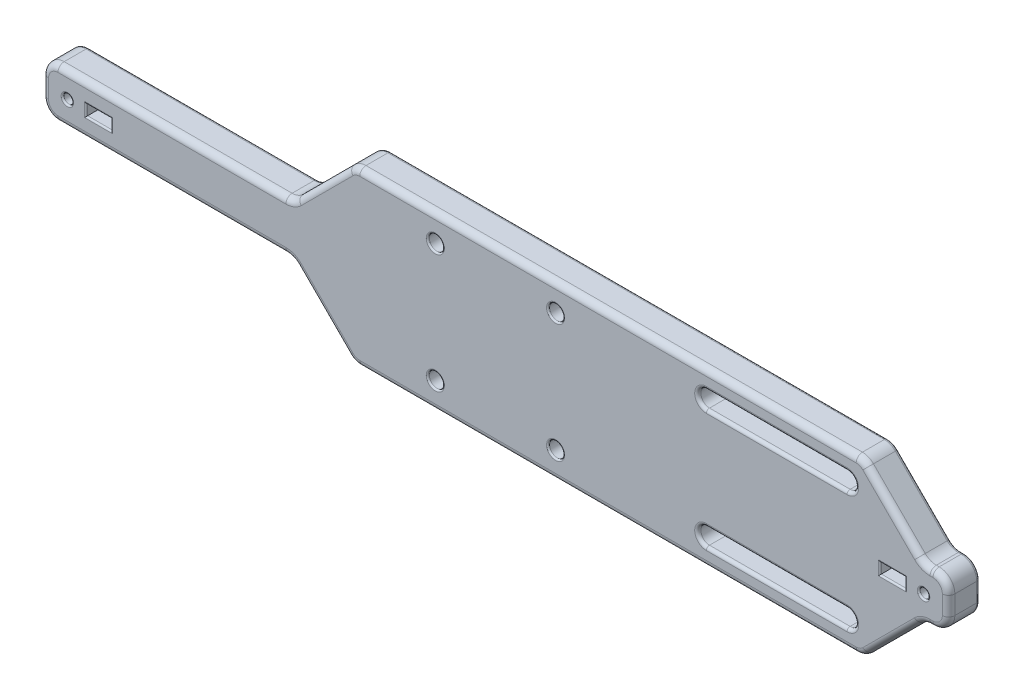
SolidWorks part; units mm, degrees
ref_plane "Спереди" through (0, 0, 0) normal (0, 0, 1) x (1, 0, 0)
ref_plane "Сверху" through (0, 0, 0) normal (0, 1, 0) x (1, 0, 0)
ref_plane "Справа" through (0, 0, 0) normal (1, 0, 0) x (0, 0, -1)
other "Configuration Table"
sketch "Sketch1" plane through (0, 0, 0) normal (0, 0, 1) x (1, 0, 0)
  line L1 (-145, -27.5) -> (145, -27.5)
  line L2 (-145, -27.5) -> (-145, 27.5)
  line L3 (-145, 27.5) -> (145, 27.5)
  line L4 (145, -27.5) -> (145, 27.5)
  line L5 (-145, -27.5) -> (145, 27.5) construction
  line L6 (-145, 27.5) -> (145, -27.5) construction
  point P0 (0, 0)
  dimension "D1" = 55
  dimension "D2" = 290
extrude "Boss-Extrude1" add sketch "Sketch1" along normal blind 10
sketch "Sketch2" plane through (0, 0, 10) normal (0, 0, 1) x (1, 0, 0)
  line L1 (-19.25, -19) -> (19.25, -19) construction
  line L2 (-19.25, -19) -> (-19.25, 19) construction
  line L3 (-19.25, 19) -> (19.25, 19) construction
  line L4 (19.25, -19) -> (19.25, 19) construction
  line L5 (-19.25, -19) -> (19.25, 19) construction
  line L6 (-19.25, 19) -> (19.25, -19) construction
  circle A0 centre (-19.25, 19) radius 2.4
  circle A1 centre (19.25, 19) radius 2.4
  circle A2 centre (19.25, -19) radius 2.4
  circle A3 centre (-19.25, -19) radius 2.4
  point P0 (0, 0)
  dimension "D3" = 4.8
  dimension "D1" = 38
  dimension "D2" = 38.5
extrude "Cut-Extrude1" cut sketch "Sketch2" against normal offset from surface (8 mm away) 2 up to face at (0, 0, 0)
sketch "Sketch4" plane through (0, 0, 10) normal (0, 0, 1) x (1, 0, 0)
  line L0 (-156.8843, 4) -> (174.6505, 4) construction
  line L1 (-19.25, 19) -> (19.25, 19) construction
  dimension "D1" = 15
sketch "Sketch5" plane through (0, 0, 10) normal (0, 0, 1) x (1, 0, 0)
  line L0 (67.5, 19) -> (112.5, 19) construction
  line L1 (67.5, 21.75) -> (112.5, 21.75)
  line L2 (67.5, 16.25) -> (112.5, 16.25)
  line L3 (0, 0) -> (27.8639, 0) construction
  line L4 (67.5, -19) -> (112.5, -19) construction
  line L5 (67.5, -21.75) -> (112.5, -21.75)
  line L6 (67.5, -16.25) -> (112.5, -16.25)
  line L7 (-19.25, 19) -> (19.25, 19) construction
  arc A0 (67.5, 21.75) -> (67.5, 16.25) centre (67.5, 19) ccw
  arc A1 (112.5, 16.25) -> (112.5, 21.75) centre (112.5, 19) ccw
  arc A2 (67.5, -21.75) -> (67.5, -16.25) centre (67.5, -19) cw
  arc A3 (112.5, -16.25) -> (112.5, -21.75) centre (112.5, -19) cw
  point P2 (90, 19)
  point P12 (90, -19)
  dimension "D1" = 5.5
  dimension "D2" = 90
  dimension "D3" = 45
extrude "Cut-Extrude2" cut sketch "Sketch5" against normal up to next
sketch "Sketch6" plane through (0, 0, 10) normal (0, 0, 1) x (1, 0, 0)
  line L0 (-156.3566, 0) -> (174.467, 0) construction
  line L1 (0, 0) -> (0, 55.5798) construction
  circle A0 centre (137, 0) radius 1.5
  circle A1 centre (-137, 0) radius 1.5
  dimension "D1" = 3
  dimension "D2" = 137
extrude "Cut-Extrude3" cut sketch "Sketch6" against normal up to next
sketch "Sketch7" plane through (0, 0, 10) normal (0, 0, 1) x (1, 0, 0)
  line L0 (-150.1, 0) -> (0, 0) construction
  line L1 (-145, 8) -> (-65, 8)
  line L2 (-145, 27.5) -> (-145, -27.5) construction
  line L3 (-65, 8) -> (-45.5, 27.5)
  line L4 (145, 27.5) -> (-145, 27.5) construction
  line L5 (-65, -8) -> (-45.5, -27.5)
  line L6 (-45.5, 27.5) -> (-145, 27.5)
  line L7 (-145, 27.5) -> (-145, 8)
  line L8 (-145, -8) -> (-65, -8)
  line L9 (-145, -27.5) -> (-145, -8)
  line L10 (-45.5, -27.5) -> (-145, -27.5)
  line L11 (117.5, 27.5) -> (137, 8)
  line L12 (137, 8) -> (145, 8)
  line L13 (145, -27.5) -> (145, 27.5) construction
  line L14 (117.5, 27.5) -> (145, 27.5)
  line L15 (145, 27.5) -> (145, 8)
  line L18 (117.5, -27.5) -> (145, -27.5)
  line L19 (117.5, -27.5) -> (137, -8)
  line L20 (137, -8) -> (145, -8)
  line L21 (145, -27.5) -> (145, -8)
  line L22 (0, 0) -> (165.838, 0) construction
  dimension "D1" = 135
  dimension "D2" = 8
  dimension "D3" = 80
  dimension "D4" = 135
  dimension "D5" = 8
  dimension "D6" = 5
extrude "Cut-Extrude4" cut sketch "Sketch7" against normal up to next
sketch "Sketch8" plane through (0, 0, 0) normal (0, 0, -1) x (-1, 0, 0)
  line L0 (0, 0) -> (0, 46.9184) construction
  line L1 (0, 0) -> (55.4328, 0) construction
  circle A0 centre (35, 15) radius 2
  circle A1 centre (35, -15) radius 2
  circle A2 centre (-35, -15) radius 2
  circle A3 centre (-35, 15) radius 2
  dimension "D1" = 4
  dimension "D2" = 15
  dimension "D3" = 35
extrude "Cut-Extrude5" cut sketch "Sketch8" against normal offset from surface (8 mm away) 2 up to face at (138.5, 0, 10)
sketch "Sketch10" plane through (0, 0, 0) normal (0, 0, -1) x (-1, 0, 0)
  circle A0 centre (-137, 0) radius 3
  circle A1 centre (137, 0) radius 3
  point P5 (134.0497, -1.5)
  point P6 (137, 0)
  point P7 (0, 0)
  dimension "D1" = 6
extrude "Cut-Extrude6" cut sketch "Sketch10" against normal offset from surface (6 mm away) 4 up to face at (138.5, 0, 10)
sketch "Sketch11" plane through (0, 0, 10) normal (0, 0, 1) x (1, 0, 0)
  line L0 (-137, 0) -> (-122.7647, 0) construction
  line L1 (0, 0) -> (0, 34.3132) construction
  line L2 (-131, -1.75) -> (-123, -1.75)
  line L3 (-131, -1.75) -> (-131, 1.75)
  line L4 (-131, 1.75) -> (-123, 1.75)
  line L5 (-123, -1.75) -> (-123, 1.75)
  line L6 (-131, -1.75) -> (-123, 1.75) construction
  line L7 (-131, 1.75) -> (-123, -1.75) construction
  line L8 (131, 1.75) -> (123, 1.75)
  line L9 (123, -1.75) -> (123, 1.75)
  line L10 (131, -1.75) -> (123, -1.75)
  line L11 (131, -1.75) -> (131, 1.75)
  point P4 (-127, 0)
  dimension "D1" = 3.5
  dimension "D2" = 10
  dimension "D3" = 8
extrude "Cut-Extrude7" cut sketch "Sketch11" against normal blind 5
fillet "Fillet2" radius 5 12 edges at (-65, -8, 5) (-45.5, -27.5, 5) (117.5, -27.5, 5) (137, -8, 5) (145, -8, 5) (145, 8, 5) (137, 8, 5) (117.5, 27.5, 5) (-45.5, 27.5, 5) (-65, 8, 5) (-145, 8, 5) (-145, -8, 5)
fillet "Fillet3" radius 0.5 22 edges at (-16.85, 19, 10) (21.65, 19, 10) (21.65, -19, 10) (-16.85, -19, 10) (138.5, 0, 10) (-138.5, 0, 10) (-37, 15, 0) (33, -15, 0) (37, 15, 0) (-33, -15, 0) (-140, 0, 0) (135.5, 0, 6) (134, 0, 0) (-138.5, 0, 6) (123, 0, 10) (127, -1.75, 10) (131, 0, 10) (127, 1.75, 10) (-123, 0, 10) (-127, -1.75, 10) (-131, 0, 10) (-127, 1.75, 10)
fillet "Fillet4" radius 2 24 edges at (117.3423, 27.1194, 10) (127.25, 17.75, 10) (137.1577, 8.3806, 10) (139.5355, 8, 10) (143.5355, 6.5355, 10) (145, 0, 10) (143.5355, -6.5355, 10) (139.5355, -8, 10) (137.1577, -8.3806, 10) (127.25, -17.75, 10) (117.3423, -27.1194, 10) (36, -27.5, 10) (-45.3423, -27.1194, 10) (-55.25, -17.75, 10) (-65.1577, -8.3806, 10) (-103.5355, -8, 10) (-143.5355, -6.5355, 10) (-145, 0, 10) (-143.5355, 6.5355, 10) (-103.5355, 8, 10) (-65.1577, 8.3806, 10) (-55.25, 17.75, 10) (-45.3423, 27.1194, 10) (36, 27.5, 10)
fillet "Fillet5" radius 1 40 edges at (64.75, -19, 10) (90, -16.25, 10) (115.25, -19, 10) (64.75, 19, 10) (90, 21.75, 10) (115.25, 19, 10) (64.75, -19, 0) (90, -16.25, 0) (115.25, -19, 0) (64.75, 19, 0) (90, 21.75, 0) (115.25, 19, 0) (117.3423, 27.1194, 0) (127.25, 17.75, 0) (137.1577, 8.3806, 0) (139.5355, 8, 0) (143.5355, 6.5355, 0) (145, 0, 0) (143.5355, -6.5355, 0) (139.5355, -8, 0) (137.1577, -8.3806, 0) (127.25, -17.75, 0) (117.3423, -27.1194, 0) (36, -27.5, 0) (-45.3423, -27.1194, 0) (-55.25, -17.75, 0) (-65.1577, -8.3806, 0) (-103.5355, -8, 0) (-143.5355, -6.5355, 0) (-145, 0, 0) (-143.5355, 6.5355, 0) (-103.5355, 8, 0) (-65.1577, 8.3806, 0) (-55.25, 17.75, 0) (-45.3423, 27.1194, 0) (90, -21.75, 10) (90, 16.25, 10) (90, -21.75, 0) (90, 16.25, 0) (36, 27.5, 0)
